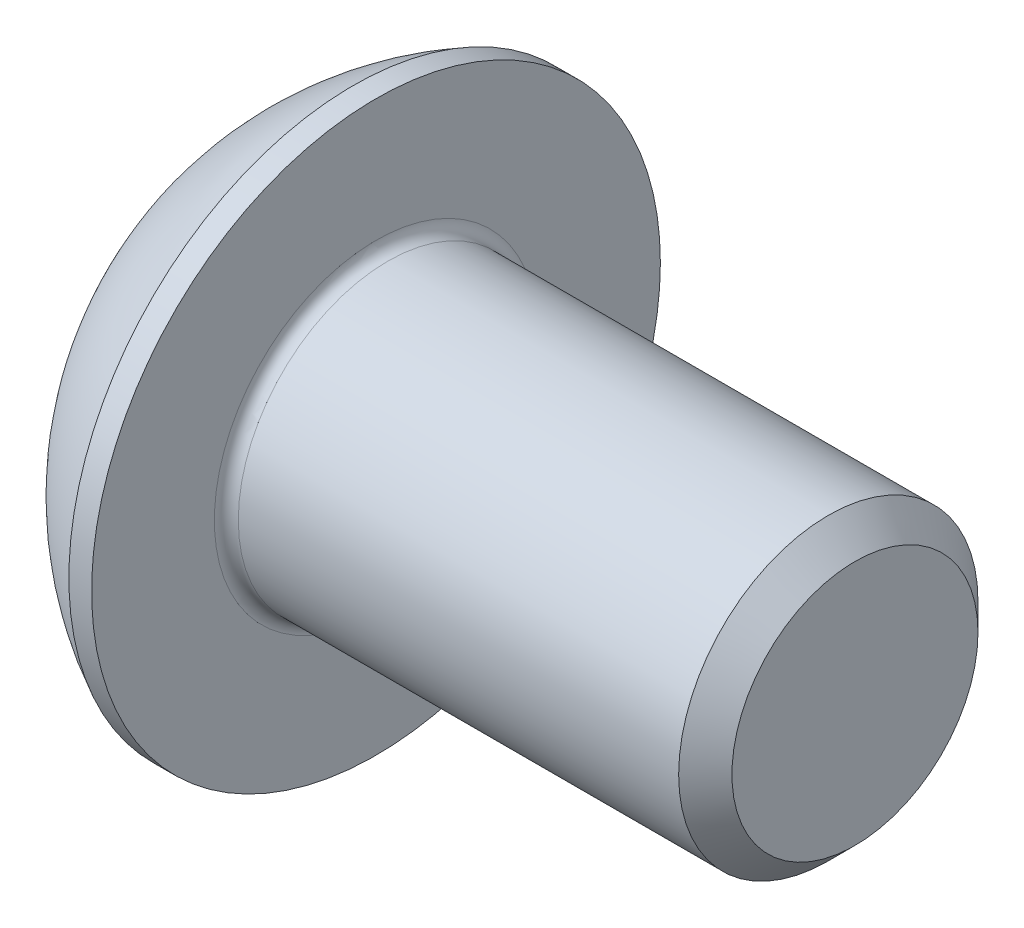
SolidWorks part; units mm, degrees
material "AISI 316 Stainless Steel Sheet (SS)"
ref_plane "Спереди" through (0, 0, 0) normal (0, 0, 1) x (1, 0, 0)
ref_plane "Сверху" through (0, 0, 0) normal (0, 1, 0) x (1, 0, 0)
ref_plane "Справа" through (0, 0, 0) normal (1, 0, 0) x (0, 0, -1)
sketch "Эскиз1" plane through (0, 0, 0) normal (0, 0, 1) x (1, 0, 0)
  line L0 (-3.6435, 0) -> (-10.508, 0) construction
  line L1 (0, 2.375) -> (0, 0)
  line L2 (0, 0) -> (10.75, 0)
  line L3 (10.75, 0) -> (10.75, 2.055)
  line L4 (10.75, 2.055) -> (10.305, 2.5)
  line L5 (10.305, 2.5) -> (2.75, 2.5)
  line L6 (2.75, 2.5) -> (2.75, 4.75)
  line L7 (2.75, 4.75) -> (2.3702, 4.75)
  arc A0 (2.3702, 4.75) -> (0, 2.375) centre (4.7549, 0) ccw
  dimension "D1" = 10.63
  dimension "D2" = 4.75
  dimension "D3" = 2.75
  dimension "D4" = 5
  dimension "D5" = 45
  dimension "D6" = 4.11
  dimension "D7" = 8
  dimension "D8" = 9.5
revolve "Body" add sketch "Эскиз1" angle 360 about L0
fillet "Chamfer" radius 0.2 1 edges at (2.75, 0, -2.5)
sketch "Эскиз2" plane through (0, 0, 0) normal (0, 0, 1) x (1, 0, 0)
  line L0 (0, 0) -> (0, 1.5)
  line L1 (0, 2.375) -> (0, -2.375) construction
  line L2 (0, 1.5) -> (1.56, 1.5)
  line L3 (1.56, 1.5) -> (2.426, 0)
  line L4 (2.426, 0) -> (0, 0)
  dimension "D1" = 1.56
  dimension "D2" = 60
  dimension "D3" = 1.5
revolve "Hole" cut sketch "Эскиз2" angle 360 about L4
sketch "Эскиз3" plane through (0, 0, 0) normal (-1, 0, 0) x (0, 0, 1)
  line L1 (-1.5, -0.866) -> (0, -1.7321)
  line L2 (0, -1.7321) -> (1.5, -0.866)
  line L3 (1.5, -0.866) -> (1.5, 0.866)
  line L4 (1.5, 0.866) -> (0, 1.7321)
  line L5 (0, 1.7321) -> (-1.5, 0.866)
  line L6 (-1.5, 0.866) -> (-1.5, -0.866)
  circle A0 centre (0, 0) radius 1.5 construction
  dimension "D1" = 3
extrude "Hex" cut sketch "Эскиз3" against normal blind 1.56
